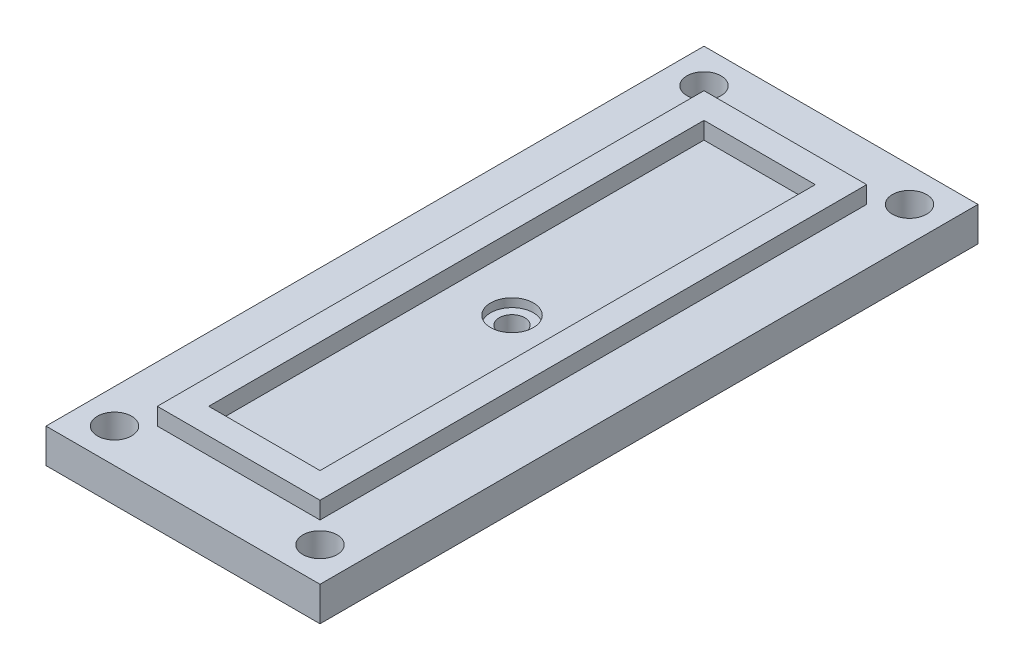
SolidWorks part; units mm, degrees
material "ABS"
ref_plane "Front Plane" through (0, 0, 0) normal (0, 0, 1) x (1, 0, 0)
ref_plane "Top Plane" through (0, 0, 0) normal (0, 1, 0) x (1, 0, 0)
ref_plane "Right Plane" through (0, 0, 0) normal (1, 0, 0) x (0, 0, -1)
sketch "Sketch1" plane through (0, 0, 0) normal (0, 1, 0) x (1, 0, 0)
  line L0 (-47.8248, 16.1021) -> (-31.8248, 16.1021) construction
  line L1 (-8, -19.21) -> (8, -19.21)
  line L2 (-8, -19.21) -> (-8, 19.21)
  line L3 (-8, 19.21) -> (8, 19.21)
  line L4 (8, -19.21) -> (8, 19.21)
  line L5 (-8, -19.21) -> (8, 19.21) construction
  line L6 (-8, 19.21) -> (8, -19.21) construction
  line L7 (-31.8248, 16.1021) -> (-31.8248, -22.3179) construction
  point P0 (0, 0)
extrude "Boss-Extrude1" add sketch "Sketch1" along normal blind 2
sketch "Sketch2" plane through (0, 2, 0) normal (0, 1, 0) x (1, 0, 0)
  line L1 (-4, -15.21) -> (4, -15.21)
  line L2 (-4, -15.21) -> (-4, 15.21)
  line L3 (-4, 15.21) -> (4, 15.21)
  line L4 (4, -15.21) -> (4, 15.21)
  line L5 (-4, -15.21) -> (4, 15.21) construction
  line L6 (-4, 15.21) -> (4, -15.21) construction
  point P0 (0, 0)
extrude "Extrude-Thin1" add sketch "Sketch2" along normal blind 1 thin thin type mid plane wall 1.5
sketch "Sketch3" plane through (0, 0, 0) normal (0, -1, 0) x (1, 0, 0)
  line L1 (8, 19.21) -> (8, -19.21) construction
  circle A0 centre (6, 17.21) radius 1
  dimension "D1" = 2
  dimension "D2" = 2
extrude "Cut-Extrude1" cut sketch "Sketch3" against normal through all
sketch "Sketch4" plane through (0, 2, 0) normal (0, 1, 0) x (1, 0, 0)
  line L0 (4.75, 0) -> (-4.75, 0) construction
  line L1 (4.75, -15.96) -> (4.75, 15.96) construction
  line L2 (-4.75, 15.96) -> (-4.75, -15.96) construction
  line L3 (0, 14.46) -> (0, -14.46) construction
  line L4 (3.25, 14.46) -> (-3.25, 14.46) construction
  line L5 (-3.25, -14.46) -> (3.25, -14.46) construction
ref_plane "Plane1" through (0, 0, 0) normal (-1, 0, 0) x (0, 0, 1)
ref_plane "Plane2" through (0, 0, 0) normal (0, 0, -1) x (-1, 0, 0)
mirror "Mirror1" about plane through (0, 0, 0) normal (0, 0, -1) of "Cut-Extrude1"
mirror "Mirror2" about plane through (0, 0, 0) normal (-1, 0, 0) of "Mirror1", "Cut-Extrude1"
sketch "Sketch5" plane through (0, 2, 0) normal (0, 1, 0) x (1, 0, 0)
  circle A0 centre (0, 0) radius 0.75
  dimension "D1" = 1.5
extrude "Cut-Extrude2" cut sketch "Sketch5" against normal through all and the other way through all
sketch "Sketch6" plane through (0, 2, 0) normal (0, 1, 0) x (1, 0, 0)
  circle A0 centre (0, 0) radius 1.25
  dimension "D1" = 2.5
extrude "Cut-Extrude6" cut sketch "Sketch6" against normal blind 0.5 contours A0
sketch "Sketch7" plane through (0, 0, 0) normal (0, -1, 0) x (1, 0, 0)
  circle A0 centre (0, 0) radius 1.5
  dimension "D1" = 3
extrude "Boss-Extrude2" add sketch "Sketch7" along normal blind 1
sketch "Sketch9" plane through (0, -1, 0) normal (0, -1, 0) x (1, 0, 0)
  circle A0 centre (0, 0) radius 0.25
  dimension "D1" = 0.5
extrude "Cut-Extrude7" cut sketch "Sketch9" against normal blind 2
